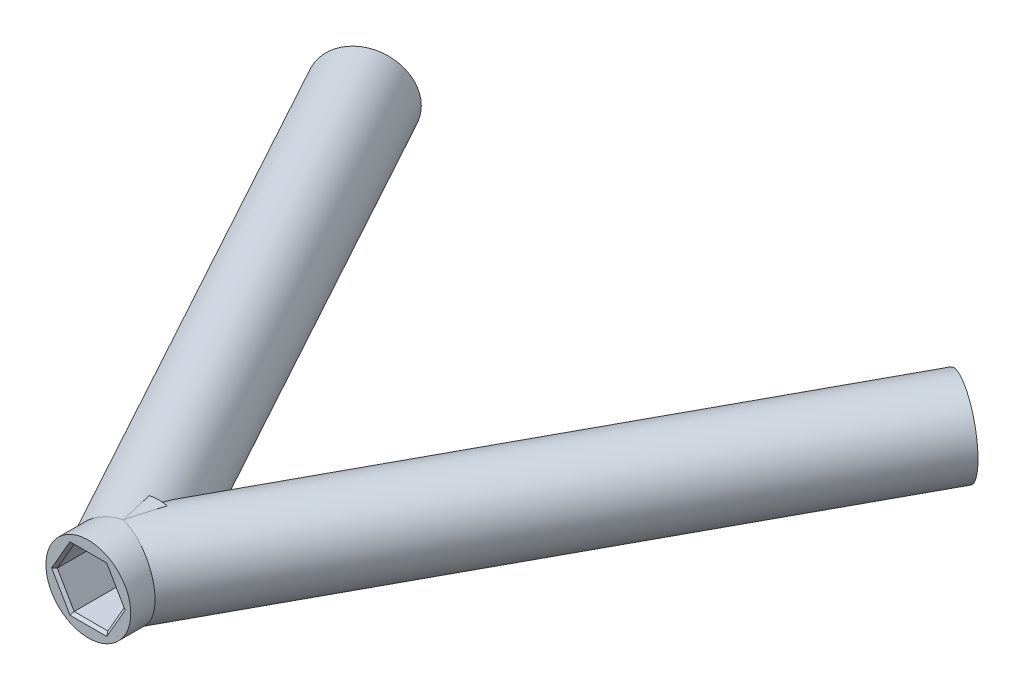
SolidWorks part; units mm, degrees
material "ABS"
ref_plane "Front Plane" through (0, 0, 0) normal (0, 0, 1) x (1, 0, 0)
ref_plane "Top Plane" through (0, 0, 0) normal (0, 1, 0) x (1, 0, 0)
ref_plane "Right Plane" through (0, 0, 0) normal (1, 0, 0) x (0, 0, -1)
sketch "Sketch1" plane through (0, 0, 0) normal (0, 1, 0) x (1, 0, 0)
  line L0 (0, 0) -> (36.1712, 87.3251) construction
  line L1 (0, 0) -> (-35.6584, 86.0871) construction
  line L2 (0, 0) -> (0, 97.1253) construction
  line L11 (0, 0) -> (0, -18.024) construction
  line L12 (0, 17.5) -> (0, 24.1)
  point P3 (-24.5606, 59.2946)
  point P6 (25.0734, 60.5326)
  point P8 (0, 17.5)
  point P9 (-27.0863, 65.3922)
  point P10 (27.5991, 66.6302)
  point P26 (0, 15.6788)
  point P27 (31.3933, 91.469)
  point P28 (36.9366, 89.1729)
  point P29 (42.4799, 86.8768)
  point P30 (0, -15.6788)
  dimension "D8" = 17.5
  dimension "D10" = 22.4
  dimension "D1" = 94.52
  dimension "D2" = 93.18
  dimension "D3" = 45
  dimension "D4" = 22.5
  dimension "D5" = 29
  dimension "D6" = 29
  dimension "D7" = 6.6
  dimension "D9" = 22.4
revolve "Revolve-Thin1" add sketch "Sketch1" angle 360 about L12 wall 4
sketch "Sketch18" plane through (0, 0, -17.5) normal (0, 0, 1) x (1, 0, 0)
  line L1 (1.5877, 2.75) -> (-1.5877, 2.75)
  line L2 (-1.5877, 2.75) -> (-3.1754, 0)
  line L3 (-3.1754, 0) -> (-1.5877, -2.75)
  line L4 (-1.5877, -2.75) -> (1.5877, -2.75)
  line L5 (1.5877, -2.75) -> (3.1754, 0)
  line L6 (3.1754, 0) -> (1.5877, 2.75)
  circle A0 centre (0, 0) radius 2.75 construction
  dimension "D1" = 5.5
sketch "Sketch19" plane through (0, 0, 0) normal (0, 1, 0) x (1, 0, 0)
  line L0 (0, 17.5) -> (0, 24.1) construction
  line L1 (0, 17.5) -> (0, 24.1) construction
  line L2 (-35.6584, 86.0871) -> (0, 20.8) construction
  line L3 (0, 20.8) -> (36.1712, 87.3251) construction
  line L5 (-27.27, 70.7286) -> (0, 20.8)
  point P2 (0, 20.8)
  point P6 (-27.27, 70.7286)
  point P9 (27.8118, 71.9507)
  dimension "D1" = 17.5
  dimension "D2" = 17.5
sketch "Sketch20" plane through (0, 0, 0) normal (0, 1, 0) x (1, 0, 0)
  line L0 (36.1712, 87.3251) -> (0, 20.8) construction
  line L1 (0, 17.5) -> (0, 24.1) construction
  line L2 (25.4712, 67.6459) -> (0, 20.8)
  point P5 (25.4712, 67.6459)
  dimension "D1" = 22.4
sketch3d "3DSketch1"
  line L0 (-27.27, 0, -70.7286) -> (0, 0, -20.8) construction
sketch "Sketch21" plane through (-36.0202, 0, -65.9494) normal (0.4793, 0, 0.8776) x (0.8776, 0, -0.4793)
  circle A0 centre (9.9703, 0) radius 4
  dimension "D1" = 8
extrude "Boss-Extrude1" add sketch "Sketch21" along normal up to next
sketch3d "3DSketch2"
  line L0 (0, 0, -20.8) -> (36.1712, 0, -87.3251) construction
sketch "Sketch22" plane through (36.5407, 0, -67.2046) normal (-0.4777, 0, 0.8785) x (0.8785, 0, 0.4777)
  circle A0 centre (-9.9357, 0) radius 4
  dimension "D1" = 8
extrude "Boss-Extrude2" add sketch "Sketch22" along normal up to next
sketch "Sketch24" plane through (0, 0, -24.1) normal (0, 0, -1) x (-1, 0, 0)
sketch3d "3DSketch3"
  line L0 (0, 0, 0) -> (0, 0, -97.1253) construction
  line L1 (0, 0, 0) -> (-35.6584, 0, -86.0871) construction
sketch "Sketch29" plane through (-36.0202, 0, -65.9494) normal (-0.4793, 0, -0.8776) x (-0.8776, 0, 0.4793)
  line L0 (-9.9703, 4) -> (-9.9703, -4) construction
  line L1 (-7.0313, 1.2022) -> (-9.5419, 3.1464)
  line L2 (-9.5419, 3.1464) -> (-12.481, 1.9442)
  line L3 (-12.481, 1.9442) -> (-12.9094, -1.2022)
  line L4 (-12.9094, -1.2022) -> (-10.3987, -3.1464)
  line L5 (-10.3987, -3.1464) -> (-7.4596, -1.9442)
  line L6 (-7.4596, -1.9442) -> (-7.0313, 1.2022)
  line L7 (-13.9703, 0) -> (-5.9703, 0) construction
  line L8 (-9.5419, 3.1464) -> (-10.3987, -3.1464) construction
  circle A0 centre (-9.9703, 0) radius 2.75 construction
  circle A1 centre (-9.9703, 0) radius 4 construction
  arc A2 (-11.5494, 3.6751) -> (-11.5494, -3.6751) centre (-9.9703, 0) ccw construction
  point P19 (-9.4288, 3.1699)
  dimension "D1" = 5.5
  dimension "D2" = 7.753
extrude "Cut-Extrude3" cut sketch "Sketch29" against normal blind 6.6
sketch "Sketch30" plane through (36.5407, 0, -67.2046) normal (0.4777, 0, -0.8785) x (-0.8785, 0, -0.4777)
  line L0 (9.9357, 4) -> (9.9357, -4) construction
  line L1 (12.8748, 1.2022) -> (10.3641, 3.1464)
  line L2 (10.3641, 3.1464) -> (7.4251, 1.9442)
  line L3 (7.4251, 1.9442) -> (6.9967, -1.2022)
  line L4 (6.9967, -1.2022) -> (9.5074, -3.1464)
  line L5 (9.5074, -3.1464) -> (12.4464, -1.9442)
  line L6 (12.4464, -1.9442) -> (12.8748, 1.2022)
  line L7 (5.9357, 0) -> (13.9357, 0) construction
  line L8 (10.3641, 3.1464) -> (9.5074, -3.1464) construction
  circle A0 centre (9.9357, 0) radius 2.75 construction
  circle A1 centre (9.9357, 0) radius 4 construction
  arc A2 (9.9357, 4) -> (9.9357, -4) centre (9.9357, 0) ccw construction
  arc A3 (11.5148, -3.6751) -> (11.5148, 3.6751) centre (9.9357, 0) ccw construction
  dimension "D1" = 5.5
  dimension "D2" = 7.753
extrude "Cut-Extrude4" cut sketch "Sketch30" against normal blind 6.6
extrude "Cut-Extrude5" cut sketch "Sketch18" against normal blind 6.6
chamfer "Chamfer2" distance 0.25 angle 45 18 edges at (0, 2.75, -17.5) (2.3816, 1.375, -17.5) (2.3816, -1.375, -17.5) (0, -2.75, -17.5) (-2.3816, -1.375, -17.5) (-2.3816, 1.375, -17.5) (-29.6614, -0.371, -69.4225) (-28.1837, -2.5453, -70.2295) (-25.7923, -2.1743, -71.5357) (-24.8785, 0.371, -72.0347) (-26.3562, 2.5453, -71.2277) (-28.7476, 2.1743, -69.9215) (25.418, -0.371, -73.2524) (26.8972, -2.5453, -72.4481) (29.291, -2.1743, -71.1465) (30.2057, 0.371, -70.6491) (28.7265, 2.5453, -71.4534) (26.3326, 2.1743, -72.755)
